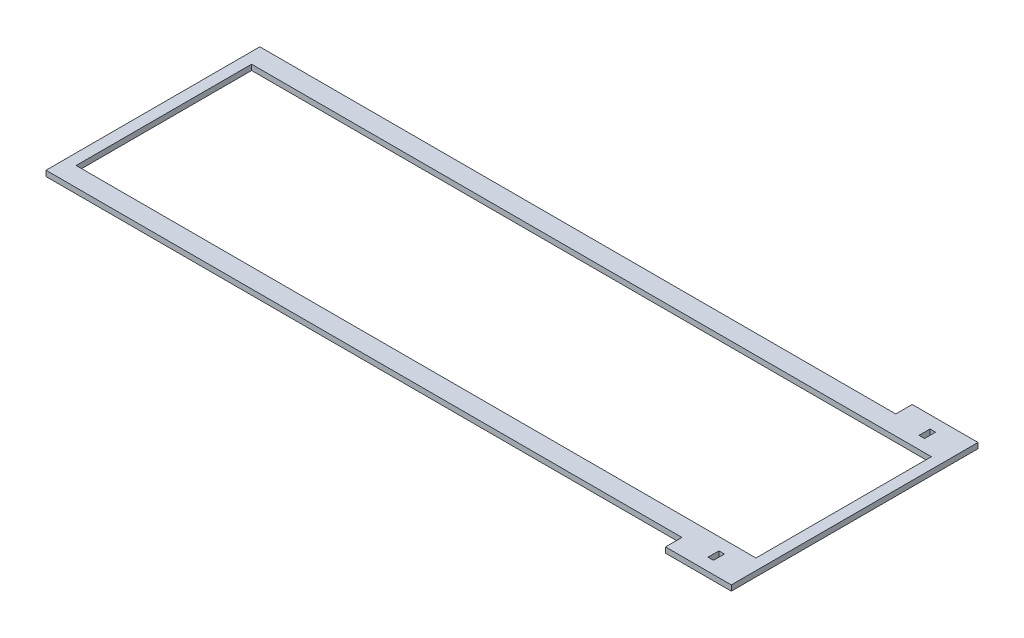
SolidWorks part; units mm, degrees
ref_plane "Front Plane" through (0, 0, 0) normal (0, 0, 1) x (1, 0, 0)
ref_plane "Top Plane" through (0, 0, 0) normal (0, 1, 0) x (1, 0, 0)
ref_plane "Right Plane" through (0, 0, 0) normal (1, 0, 0) x (0, 0, -1)
sketch "Sketch1" plane through (0, 0, 0) normal (0, 1, 0) x (1, 0, 0)
  line L0 (-203.2, 0) -> (203.2, 0) construction
  line L1 (165.1, 71.4375) -> (203.2, 71.4375)
  line L3 (165.1, -71.4375) -> (203.2, -71.4375)
  line L4 (203.2, 71.4375) -> (203.2, -71.4375)
  line L5 (-203.2, 71.4375) -> (203.2, -71.4375) construction
  line L6 (-203.2, -71.4375) -> (203.2, 71.4375) construction
  line L7 (-203.2, -71.4375) -> (165.1, -71.4375) construction
  line L8 (-203.2, -71.4375) -> (-203.2, -61.9125) construction
  line L9 (-203.2, -61.9125) -> (165.1, -61.9125)
  line L10 (165.1, -71.4375) -> (165.1, -61.9125)
  line L11 (-203.2, 71.4375) -> (165.1, 71.4375) construction
  line L12 (-203.2, 71.4375) -> (-203.2, 61.9125) construction
  line L13 (-203.2, 61.9125) -> (165.1, 61.9125)
  line L14 (165.1, 71.4375) -> (165.1, 61.9125)
  line L15 (-196.85, 50.8) -> (-196.85, -50.8)
  line L16 (196.85, 50.8) -> (-196.85, 50.8)
  line L17 (203.2, 50.8) -> (203.2, -50.8)
  line L18 (196.85, -50.8) -> (-196.85, -50.8)
  line L19 (-203.2, 50.8) -> (-203.2, -50.8)
  line L20 (196.85, 50.8) -> (196.85, -50.8)
  line L21 (-196.85, -50.8) -> (-203.2, -50.8) construction
  line L22 (-196.85, 50.8) -> (-203.2, 50.8) construction
  line L23 (203.2, 50.8) -> (196.85, 50.8) construction
  line L24 (203.2, -50.8) -> (196.85, -50.8) construction
  line L25 (-203.2, -71.4375) -> (165.1, -71.4375) construction
  line L26 (185.7375, -57.9438) -> (182.5625, -57.9438)
  line L27 (185.7375, -57.9438) -> (185.7375, -64.2938)
  line L28 (185.7375, -64.2938) -> (182.5625, -64.2938)
  line L29 (182.5625, -57.9438) -> (182.5625, -64.2938)
  line L30 (-203.2, 71.4375) -> (165.1, 71.4375) construction
  line L31 (185.7375, -50.8) -> (185.7375, -71.4375) construction
  line L32 (185.7375, 64.2938) -> (182.5625, 64.2938)
  line L33 (182.5625, 57.9438) -> (182.5625, 64.2938)
  line L34 (185.7375, 57.9438) -> (182.5625, 57.9438)
  line L35 (185.7375, 57.9438) -> (185.7375, 64.2938)
  line L36 (-203.2, 61.9125) -> (-203.2, 50.8)
  line L37 (-203.2, -50.8) -> (-203.2, -61.9125)
  point P0 (0, 0)
  point P18 (203.2, 0)
  point P27 (184.15, -64.2938)
  point P28 (184.15, -71.4375)
  point P31 (185.7375, -61.1187)
  point P32 (185.7375, -61.1187)
  point P37 (-196.85, 0)
  dimension "D3" = 38.1
  dimension "D4" = 123.825
  dimension "D6" = 101.6
  dimension "D8" = 6.35
  dimension "D9" = 3.175
  dimension "D10" = 6.35
  dimension "D7" = 165.1
  dimension "D11" = 196.85
  dimension "d2" = 142.875
extrude "Boss-Extrude1" add sketch "Sketch1" along normal mid plane 3.175
equation "\"D3@Sketch1\"=1.50in"
equation "\"m\"=5"
equation "\"TabWidth\"=5.625"
equation "\"d2@Sketch1\" = \"TabWidth\""
equation "\"RoadWidth\"= 5.625"
